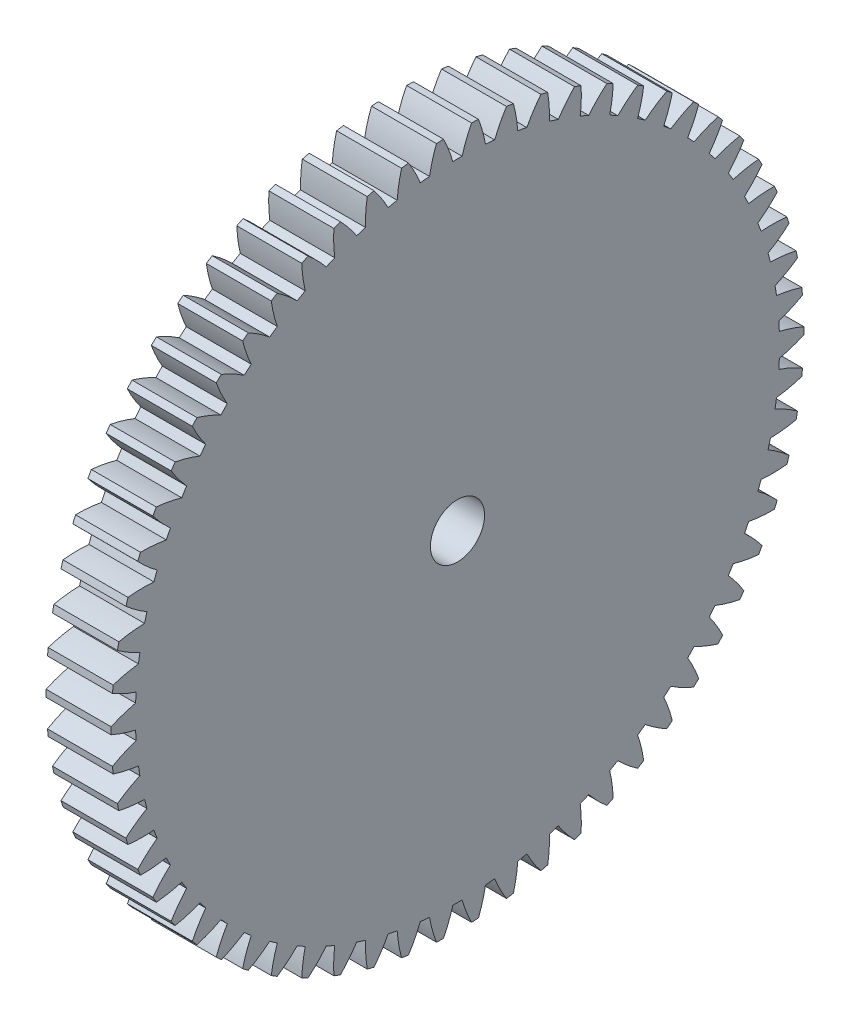
SolidWorks part; units mm, degrees
ref_plane "Plane1" through (0, 0, 0) normal (0, 0, 1) x (1, 0, 0)
ref_plane "Plane2" through (0, 0, 0) normal (0, 1, 0) x (1, 0, 0)
ref_plane "Plane3" through (0, 0, 0) normal (1, 0, 0) x (0, 0, -1)
sketch "HoldingSke" plane through (0, 0, 0) normal (0, 1, 0) x (1, 0, 0)
  line L0 (0, 0) -> (0.9389, -1.7659)
  line L1 (-15, 0) -> (100, 0) construction
  line L2 (0, 0) -> (-2.1039, 2.3779)
  line L3 (0, 0) -> (-11.863, 4.5341)
  line L4 (0, 0) -> (4.0544, 7.6251)
  line L5 (0, 0) -> (-46.8476, -17.4728)
  line L6 (0, 0) -> (-2.4869, -1.6779)
  line L7 (-2.1039, 2.3779) -> (8.6586, 51.2059)
  line L8 (-76.2, 54.61) -> (-76, 54.61)
  line L9 (-71.009, 38.7566) -> (-53.1078, 45.2721)
  line L10 (-76.2, 71.12) -> (104.1128, 71.12)
  line L11 (0, 0) -> (-3, 0)
  line L12 (-76.2, 101.6) -> (-76.181, 101.6)
  line L13 (24.9733, 27.94) -> (52.9518, 28.4284)
  line L14 (24.9733, 27.94) -> (24.9743, 27.94)
  line L15 (24.9733, 27.94) -> (100.4006, 29.5858)
  line L16 (-63.627, -0.5) -> (-12.827, -0.5)
  circle A0 centre (0, 0) radius 0.75
  circle A1 centre (0, 0) radius 14.874
  circle A2 centre (0, 0) radius 37.5
  circle A3 centre (0, 0) radius 0.75
  dimension "MHD" = 29.748
  dimension "Hub_dia" = 75
  dimension "Bore" = 1.5
  dimension "MBD" = 1.5
  dimension "Num_teeth" = 62
  dimension "Pitch" = 2
  dimension "Overall_len" = 50
  dimension "Show_teeth" = 62
  dimension "Thickness" = 3
  dimension "OAL" = 50.0001
  dimension "T_dim" = 0.2
  dimension "Ap" = 20
  dimension "H" = 19.05
  dimension "Pitch_radius" = 180.3128
  dimension "Width" = 3
  dimension "Backlash" = 0.019
  dimension "Addendum_fac" = 1
  dimension "Dedendum_fac" = 1.25
  dimension "Clearance_fac" = 0.25
  dimension "Dedendum_add" = 0.001
  dimension "Module" = 0.5
sketch "BasProSke" plane through (0, 0, 0) normal (0, 1, 0) x (1, 0, 0)
  line L0 (-10, 0) -> (60, 0) construction
  line L1 (0, 0) -> (0, 16)
  line L2 (0, 0) -> (3, 0)
  line L3 (3, 0) -> (3, 16)
  line L4 (3, 16) -> (0, 16)
  dimension "Thickness" = 3
  dimension "Diameter" = 32
revolve "Base-Revolve" add sketch "BasProSke" angle 360 about L0
sketch "TooCutSke" plane through (0, 0, 0) normal (1, 0, 0) x (0, 0, -1)
  line L1 (0, 0) -> (0, 107) construction
  line L2 (0, 0) -> (-0.4259, 15.4941) construction
  line L3 (0, 0) -> (-1.5697, 30.9519) construction
  line L4 (-0.4259, 15.4941) -> (-0.7849, 15.4759) construction
  arc A0 (0.2143, 14.8725) -> (-0.2143, 14.8725) centre (0, 0) ccw
  arc A1 (0.6613, 16.0117) -> (-0.6613, 16.0117) centre (0, 0) ccw
  circle A2 centre (0, 0) radius 15.5 construction
  circle A3 centre (0, 0) radius 14.5652 construction
  arc A4 (-0.2143, 14.8725) -> (-0.6613, 16.0117) centre (-6.1813, 13.1886) ccw
  arc A5 (0.6613, 16.0117) -> (0.2143, 14.8725) centre (6.1813, 13.1886) ccw
  dimension "Root_dia" = 29.748
  dimension "Overcut_dia" = 32.0508
  dimension "Pitch_dia" = 31
  dimension "Base_dia" = 29.1305
  dimension "Flank_rad" = 6.2
  dimension "Half_ang" = 2.903
  dimension "Half_CT" = 0.3594
extrude "ToothCut" cut sketch "TooCutSke" along normal through all
fillet "Breaks" [suppressed] radius 0.01
fillet "RootFillets" [suppressed] radius 0.126
pattern_circular "TeethCuts" count 62 every 5.806 about axis through (-10, 0, 0) along (1, 0, 0) of "ToothCut", "RootFillets", "Breaks"
sketch "HubNeaOneSke" plane through (0, 0, 0) normal (-1, 0, 0) x (0, 0, 1)
  circle A0 centre (0, 0) radius 14.874
  dimension "Diameter" = 29.748
extrude "HubNearOne" [suppressed] add sketch "HubNeaOneSke" along normal blind 47.0001
sketch "HubNeaBotSke" plane through (0, 0, 0) normal (-1, 0, 0) x (0, 0, 1)
  circle A0 centre (0, 0) radius 14.874
  dimension "Diameter" = 29.748
extrude "HubNearBoth" [suppressed] add sketch "HubNeaBotSke" along normal blind 23.5
ref_plane "FarPln" through (3, 0, 0) normal (1, 0, 0) x (0, 0, -1)
sketch "HubFarSke" plane through (3, 0, 0) normal (1, 0, 0) x (0, 0, -1)
  circle A0 centre (0, 0) radius 14.874
  dimension "Diameter" = 29.748
extrude "HubFar" [suppressed] add sketch "HubFarSke" along normal blind 23.5
sketch "BorSke" plane through (0, 0, 0) normal (1, 0, 0) x (0, 0, -1)
  circle A0 centre (0, 0) radius 0.75
  dimension "Diameter" = 1.5
extrude "Bore" cut sketch "BorSke" along normal mid plane 100.0001
sketch "KeySke" plane through (0, 0, 0) normal (1, 0, 0) x (0, 0, -1)
  line L0 (-0.3, 0) -> (-0.3, 0.95)
  line L1 (-0.3, 0.95) -> (0.3, 0.95)
  line L2 (0.3, 0.95) -> (0.3, 0)
  line L3 (0, 0) -> (0, 34) construction
  line L4 (-0.3, 0) -> (0.3, 0)
  dimension "Offset" = 0.95
  dimension "Width" = 0.6
extrude "Keyway" [suppressed] cut sketch "KeySke" along normal mid plane 100.0001
pattern_circular "Keyway2" [suppressed] count 2 every 90 about axis through (-10, 0, 0) along (1, 0, 0)
sketch "Sketch1" plane through (3, 0, 0) normal (1, 0, 0) x (0, 0, -1)
  circle A0 centre (0, 0) radius 1.25
  dimension "D1" = 2.5
extrude "Cut-Extrude1" cut sketch "Sketch1" against normal blind 10
equation "' \"Module@HoldingSke\" = 6.35"
equation "' \"Num_teeth@HoldingSke\" = 12"
equation "' \"Ap@HoldingSke\" =  20"
equation "' \"Ap@HoldingSke\" = 20"
equation "' \"Width@HoldingSke\" = 0.5 * 25.4"
equation "' \"Hub_dia@HoldingSke\"= 1 * 25.4"
equation "' \"Hub_dia@HoldingSke\" = 1 * 25.4"
equation "' \"Overall_len@HoldingSke\" = 1.0 * 25.4"
equation "' \"Bore@HoldingSke\" = 0.75 * 25.4"
equation "' \"T_dim@HoldingSke\" = 0.1 * 25.4"
equation "' \"Width@KeySke\" = 0.25 * 25.4"
equation "' \"Show_teeth@HoldingSke\" = 13"
equation "' \"Backlash@HoldingSke\" = 0.009 * 25.4"
equation "' \"Addendum_fac@HoldingSke\" = 1.0"
equation "' \"Dedendum_fac@HoldingSke\" = 1.25"
equation "' \"Dedendum_add@HoldingSke\" = 0.00005 * 25.4"
equation "' \"Clearance_fac@HoldingSke\" = 0.25"
equation "\"Pitch@HoldingSke\" = 1 / \"Module@HoldingSke\""
equation "\"Overcut_dia@TooCutSke\" = (\"Num_teeth@HoldingSke\" + 2 * \"Addendum_fac@HoldingSke\") / \"Pitch@HoldingSke\" + 0.002 * 25.4"
equation "\"Pitch_dia@TooCutSke\" = \"Num_teeth@HoldingSke\" / \"Pitch@HoldingSke\""
equation "\"Base_dia@TooCutSke\" = \"Num_teeth@HoldingSke\" / \"Pitch@HoldingSke\" * cos((\"Ap@HoldingSke\"  * 3.14159265 / 180))"
equation "\"Root_dia@TooCutSke\" = (\"Num_teeth@HoldingSke\" + 2) / \"Pitch@HoldingSke\" - 2 * (\"Addendum_fac@HoldingSke\" + \"Dedendum_fac@HoldingSke\") / \"Pitch@HoldingSke\" - \"Dedendum_add@HoldingSke\" * 2"
equation "\"Half_ang@TooCutSke\" = 180 / \"Num_teeth@HoldingSke\""
equation "\"Half_CT@TooCutSke\" = \"Num_teeth@HoldingSke\" / \"Pitch@HoldingSke\" * sin((3.14159265 / 2 / \"Num_teeth@HoldingSke\")) / 2 - 7 * \"Backlash@HoldingSke\" / 4"
equation "\"Flank_rad@TooCutSke\" = \"Num_teeth@HoldingSke\" / \"Pitch@HoldingSke\" / 5"
equation "\"Radius@RootFillets\" = \"Clearance_fac@HoldingSke\" / \"Pitch@HoldingSke\" + \"Dedendum_add@HoldingSke\""
equation "\"Break_rad@Breaks\" = 0.02 / \"Pitch@HoldingSke\""
equation "\"Thickness@HoldingSke\" = \"Width@HoldingSke\""
equation "\"OAL@HoldingSke\" = \"Thickness@HoldingSke\""
equation "\"MHD@HoldingSke\" = (\"Num_teeth@HoldingSke\" + 2) / \"Pitch@HoldingSke\" - 2 * (\"Addendum_fac@HoldingSke\" + \"Dedendum_fac@HoldingSke\")  / \"Pitch@HoldingSke\" - \"Dedendum_add@HoldingSke\" * 2"
equation "\"MBD@HoldingSke\" = (\"Num_teeth@HoldingSke\" + 2) / \"Pitch@HoldingSke\" - 2 * (\"Addendum_fac@HoldingSke\" + \"Dedendum_fac@HoldingSke\")  / \"Pitch@HoldingSke\" - \"Dedendum_add@HoldingSke\" * 2 - 0.002 * 25.4"
equation "\"MHD@HoldingSke\" = ((sgn( \"MHD@HoldingSke\" - \"Hub_dia@HoldingSke\" )-1)*( \"MHD@HoldingSke\" - \"Hub_dia@HoldingSke\" ))/-2+ \"Hub_dia@HoldingSke\""
equation "\"MBD@HoldingSke\" = ((sgn( \"MBD@HoldingSke\" - \"Bore@HoldingSke\" )-1)*( \"MBD@HoldingSke\" - \"Bore@HoldingSke\" ))/-2+ \"Bore@HoldingSke\""
equation "\"OAL@HoldingSke\" = ((sgn( \"OAL@HoldingSke\" - \"Overall_len@HoldingSke\" )+1)*( \"OAL@HoldingSke\" - \"Overall_len@HoldingSke\" ))/2 + \"Overall_len@HoldingSke\" + 0.000002 * 25.4"
equation "\"Num_teeth@TeethCuts\" = int( \"Show_teeth@HoldingSke\" ) + 1"
equation "\"Num_teeth@TeethCuts\" = ((sgn( \"Num_teeth@TeethCuts\" - \"Num_teeth@HoldingSke\" )-1)*( \"Num_teeth@TeethCuts\" - \"Num_teeth@HoldingSke\" ))/-2+ \"Num_teeth@HoldingSke\""
equation "\"Num_teeth@TeethCuts\" = ((sgn( \"Num_teeth@TeethCuts\" - 2.0)+1)*( \"Num_teeth@TeethCuts\" - 2.0))/2 +2.0"
equation "\"Angle@TeethCuts\" = 360.0 / \"Num_teeth@HoldingSke\""
equation "\"Diameter@BasProSke\" = (\"Num_teeth@HoldingSke\" + 2 * \"Addendum_fac@HoldingSke\") / \"Pitch@HoldingSke\""
equation "\"Thickness@BasProSke\"  = \"Thickness@HoldingSke\""
equation "' \"Fillet_rad@BasProSke\" =  \"Thickness@HoldingSke\" * 0.05"
equation "' \"Fillet_rad@BasProSke\" = \"Thickness@HoldingSke\" * 0.05"
equation "\"MHD@HoldingSke\" = ((sgn( \"MHD@HoldingSke\" - \"Root_dia@TooCutSke\" )-1)*( \"MHD@HoldingSke\" - \"Root_dia@TooCutSke\" ))/-2+ \"Root_dia@TooCutSke\""
equation "\"Diameter@HubNeaOneSke\" = \"MHD@HoldingSke\""
equation "\"Length@HubNearOne\" = \"OAL@HoldingSke\" - \"Thickness@BasProSke\""
equation "\"Diameter@HubNeaBotSke\" = \"MHD@HoldingSke\""
equation "\"Length@HubNearBoth\" = ( \"OAL@HoldingSke\" - \"Thickness@BasProSke\" ) / 2.0"
equation "\"Thickness@FarPln\" = \"Thickness@BasProSke\""
equation "\"Diameter@HubFarSke\" = \"MHD@HoldingSke\""
equation "\"Length@HubFar\" = ( \"OAL@HoldingSke\" - \"Thickness@BasProSke\" ) / 2.0"
equation "\"Diameter@BorSke\" = \"MBD@HoldingSke\""
equation "\"D1@Bore\" = \"OAL@HoldingSke\" * 2.0"
equation "\"D1@Keyway\" = \"OAL@HoldingSke\" * 2.0"
equation "\"Offset@KeySke\" = \"T_dim@HoldingSke\" + \"MBD@HoldingSke\" / 2.0"
